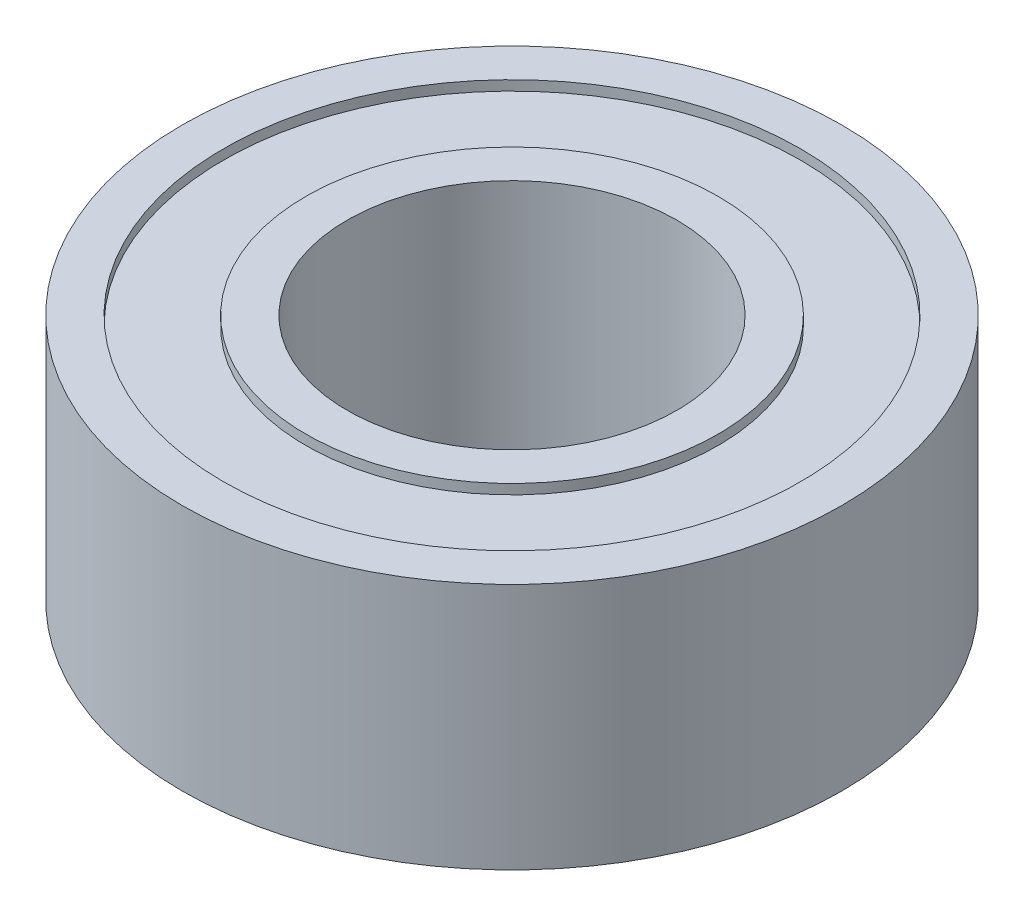
SolidWorks part; units mm, degrees
ref_plane "Front Plane" through (0, 0, 0) normal (0, 0, 1) x (1, 0, 0)
ref_plane "Top Plane" through (0, 0, 0) normal (0, 1, 0) x (1, 0, 0)
ref_plane "Right Plane" through (0, 0, 0) normal (1, 0, 0) x (0, 0, -1)
sketch "Sketch1" plane through (0, 0, 0) normal (0, 0, 1) x (1, 0, 0)
  line L0 (15.875, 9.525) -> (15.875, 8.763)
  line L1 (15.875, 8.763) -> (22.225, 8.763)
  line L2 (22.225, 8.763) -> (22.225, 9.525)
  line L3 (22.225, 9.525) -> (25.4, 9.525)
  line L4 (25.4, 9.525) -> (25.4, 0)
  line L5 (25.4, 0) -> (12.7, 0)
  line L6 (12.7, 0) -> (12.7, 9.525)
  line L7 (12.7, 9.525) -> (15.875, 9.525)
  line L8 (0, 0) -> (0, 3.9741)
  dimension "D1" = 12.7
  dimension "D2" = 25.4
  dimension "D3" = 3.175
  dimension "D4" = 0.762
  dimension "D5" = 9.525
revolve "Revolve1" add sketch "Sketch1" angle 360 about L8
mirror "Mirror1" about plane through (0, 0, 0) normal (0, 1, 0) of bodies 102
